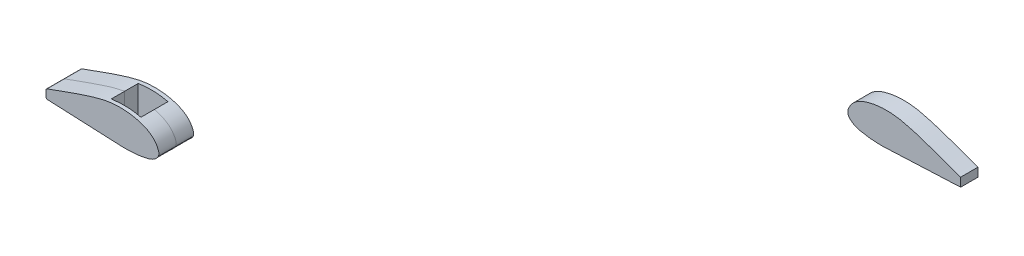
SolidWorks part; units mm, degrees
ref_plane "Front Plane" through (0, 0, 0) normal (0, 0, 1) x (1, 0, 0)
ref_plane "Top Plane" through (0, 0, 0) normal (0, 1, 0) x (1, 0, 0)
ref_plane "Right Plane" through (0, 0, 0) normal (1, 0, 0) x (0, 0, -1)
sketch "Sketch1" plane through (0, 0, 0) normal (0, 0, 1) x (1, 0, 0)
  line L0 (21.0546, 22.9864) -> (188.6881, 22.9864) construction
  line L1 (-41.685, 65.0353) -> (-41.685, -25.9647) construction
  line L3 (-116.1, 51.5887) -> (-116.1, -29.4113) construction
  line L4 (188.6881, 22.9864) -> (188.6881, 7.9864)
  spline S0 degree 3 poles (-151.9731, 22.9864) (-143.9092, 38.1196) (-120.835, 55.7856) (-80.169, 65.1927) (-35.3454, 65.9476) (18.9904, 59.1194) (95.9861, 45.5554) (152.0416, 30.4393) (188.6881, 22.9864) knots 0 0 0 0 0.141691 0.229555 0.346093 0.514874 0.687107 1 1 1 1
  spline S1 degree 3 poles (-151.9731, 22.9864) (-158.0316, 8.8512) (-149.1797, -22.7957) (-113.0152, -30.9858) (-83.4053, -30.4269) (17.4041, -20.5137) (107.6783, -0.9352) (188.6881, 7.9864) knots 0.008053 0.008053 0.008053 0.008053 0.128593 0.21014 0.276739 0.362962 1 1 1 1
  dimension "D1" = 81
  dimension "D2" = 91
  dimension "D3" = 15
  dimension "D4" = 343
sketch "Sketch2" plane through (0, 0, 0) normal (0, 0, 1) x (1, 0, 0)
  line L0 (582.2004, -1942.846) -> (4390.2004, -1942.846) construction
  line L1 (-5.98, 34.7326) -> (-5.98, -144.9211) construction
  line L2 (-106.6757, 91) -> (-106.6757, 0) construction
  line L3 (-106.6757, -0.5563) -> (-331.2996, 9.6091) construction
  line L6 (-332.8547, 9.4922) -> (-333.7996, 9.4922)
  line L7 (-331.2996, 9.6091) -> (-331.2996, 30.9254) construction
  line L8 (-106.7228, -3.0567) -> (-333.7996, 7.2197)
  line L9 (-333.7996, 7.2197) -> (-333.7996, 32.7336)
  spline S0 degree 3 poles (-331.2996, 30.9254) (-297.8418, 41.9545) (-253.3184, 59.9912) (-192.0547, 79.1992) (-150.6233, 90.2689) (-105.419, 92.3488) (-66.9278, 86.5323) (-36.0326, 74.7384) (-17.6589, 59.785) (-9.3021, 45.7524) (-5.5377, 35.7501) (-6.0018, 28.3147) (-10.6346, 20.776) (-24.032, 9.0194) (-45.4687, 4.5344) (-65.0902, 1.3964) (-83.8001, -0.2358) (-97.0071, -0.4829) (-106.6757, -0.5563) knots 0 0 0 0 0.223979 0.304379 0.408089 0.495215 0.589887 0.653497 0.703277 0.736722 0.756369 0.77031 0.782152 0.8116 0.880896 0.916077 0.938587 1 1 1 1 construction
  spline S1 degree 1 poles (-333.7996, 32.7336) (-106.7228, -3.0567) knots 0 0 1 1 construction
  spline S2 degree 3 poles (-333.7996, 32.7336) (-329.1237, 34.275) (-319.7928, 37.4124) (-301.2125, 43.9934) (-278.0532, 52.5474) (-250.2121, 62.8152) (-222.1096, 72.4601) (-193.7214, 81.1587) (-169.6947, 87.6921) (-150.0856, 91.4139) (-135.1756, 93.1815) (-120.1695, 93.9012) (-105.1423, 93.5955) (-90.1647, 92.2678) (-75.3139, 89.8335) (-60.6934, 86.2283) (-46.3415, 81.3284) (-34.9563, 75.6439) (-26.4496, 69.8498) (-20.5296, 64.8692) (-15.2153, 59.2269) (-10.6969, 52.9306) (-7.6128, 47.2762) (-5.4907, 42.5802) (-4.1355, 38.7998) (-3.3219, 34.7152) (-3.3391, 31.094) (-3.8981, 28.2134) (-4.898, 25.4017) (-6.7335, 22.3984) (-9.223, 19.2822) (-12.0263, 16.4329) (-15.0689, 13.8979) (-19.3823, 10.9122) (-25.1173, 7.9216) (-32.3596, 5.2763) (-39.8012, 3.3242) (-47.2993, 1.8347) (-54.6819, 0.548) (-62.0495, -0.6004) (-69.4829, -1.4996) (-79.4416, -2.3326) (-91.8643, -2.8893) (-101.7664, -3.0191) (-106.7228, -3.0567) knots -0.003832 -0.003832 -0.003832 -0.003832 0.027542 0.058916 0.121664 0.184413 0.247161 0.309909 0.372657 0.404031 0.435406 0.46678 0.498154 0.529528 0.560902 0.592276 0.62365 0.655024 0.670712 0.686399 0.702086 0.717773 0.73346 0.741303 0.749147 0.75699 0.764834 0.768756 0.772677 0.780521 0.788364 0.796208 0.804052 0.811895 0.827582 0.843269 0.858956 0.874643 0.89033 0.906017 0.921705 0.937392 0.968766 1.00014 1.00014 1.00014 1.00014
  dimension "D1" = 2.5
  dimension "D2" = 91
extrude "Boss-Extrude2" add sketch "Sketch2" along normal blind 50.8 separate body
fillet "Fillet2" radius 5 2 edges at (-333.7996, 7.2197, 25.4) (-333.7996, 32.7336, 25.4)
sketch "Sketch4" plane through (0, 0, 50.8) normal (0, 0, 1) x (1, 0, 0)
  line L0 (-67.2474, 87.7878) -> (-67.2474, -1.2122)
  line L1 (-154.2474, 90.5559) -> (-154.2474, -0.906)
  line L2 (-106.7228, -3.0567) -> (-329.0256, 7.0036) construction
  spline S0 degree 3 poles (-330.3793, 33.8668) (-326.848, 35.0427) (-318.6596, 37.8137) (-301.2125, 43.9934) (-278.0532, 52.5474) (-250.2121, 62.8152) (-222.1096, 72.4601) (-193.7214, 81.1587) (-169.6947, 87.6921) (-150.0856, 91.4139) (-135.1756, 93.1815) (-120.1695, 93.9012) (-105.1423, 93.5955) (-90.1647, 92.2678) (-75.3139, 89.8335) (-60.6934, 86.2283) (-46.3415, 81.3284) (-34.9563, 75.6439) (-26.4496, 69.8498) (-20.5296, 64.8692) (-15.2153, 59.2269) (-10.6969, 52.9306) (-7.6128, 47.2762) (-5.4907, 42.5802) (-4.1355, 38.7998) (-3.3219, 34.7152) (-3.3391, 31.094) (-3.8981, 28.2134) (-4.898, 25.4017) (-6.7335, 22.3984) (-9.223, 19.2822) (-12.0263, 16.4329) (-15.0689, 13.8979) (-19.3823, 10.9122) (-25.1173, 7.9216) (-32.3596, 5.2763) (-39.8012, 3.3242) (-47.2993, 1.8347) (-54.6819, 0.548) (-62.0495, -0.6004) (-69.4829, -1.4996) (-79.4416, -2.3326) (-91.8643, -2.8893) (-101.7664, -3.0191) (-106.7228, -3.0567) knots 0.003822 0.003822 0.003822 0.003822 0.027542 0.058916 0.121664 0.184413 0.247161 0.309909 0.372657 0.404031 0.435406 0.46678 0.498154 0.529528 0.560902 0.592276 0.62365 0.655024 0.670712 0.686399 0.702086 0.717773 0.73346 0.741303 0.749147 0.75699 0.764834 0.768756 0.772677 0.780521 0.788364 0.796208 0.804052 0.811895 0.827582 0.843269 0.858956 0.874643 0.89033 0.906017 0.921705 0.937392 0.968766 1.00014 1.00014 1.00014 1.00014 construction
  dimension "D1" = 87
  dimension "D2" = 89
sketch "Sketch5" plane through (0, 0, 0) normal (0, 1, 0) x (1, 0, 0)
  line L0 (-154.2474, -50.8) -> (-154.2474, -11.3)
  line L1 (-106.7228, -50.8) -> (-329.0256, -50.8) construction
  line L2 (-154.2474, -11.3) -> (-67.2474, -11.3)
  line L3 (-67.2474, -11.3) -> (-67.2474, -50.8)
  line L4 (-330.3793, -50.8) -> (-3.3709, -50.8) construction
  line L5 (-3.3709, 0) -> (-330.3793, 0) construction
  line L6 (-154.2474, -50.8) -> (-67.2474, -50.8)
  point P6 (-67.2474, -50.8)
  dimension "D1" = 87
  dimension "D2" = 11.3
extrude "Cut-Extrude1" cut sketch "Sketch5" against normal through all both and the other way through all
sketch "Sketch7" plane through (0, 0, 11.3) normal (0, 0, 1) x (1, 0, 0)
  line L0 (-154.2474, -0.906) -> (-106.7228, -3.0567) construction
  line L1 (-154.2474, -0.906) -> (-106.7228, -3.0567)
  line L2 (-154.2474, -0.906) -> (-154.2474, 4.7878)
  line L3 (-154.2474, 90.5559) -> (-154.2474, -0.906) construction
  line L4 (-154.2474, 4.7878) -> (-67.2474, 4.7878)
  line L5 (-67.2474, 87.7878) -> (-67.2474, -1.2122) construction
  line L6 (-67.2474, 4.7878) -> (-67.2474, -1.2122)
  spline S0 degree 3 poles (-2112.4086, -4538.979) (-528.9752, 150.7515) (-315.4023, -12.9058) (-79.4416, -2.3326) (172.6666, 18.7546) (361.4737, 490.2368) (-4320.865, -2623.6355) knots -0.494407 -0.494407 -0.494407 -0.494407 0.948356 0.97973 0.995417 2.536856 2.536856 2.536856 2.536856 only from (-106.7228, -3.0567) to (-67.2474, -1.2122) construction
  spline S1 degree 3 poles (-106.7228, -3.0567) (-101.7664, -3.0191) (-91.8643, -2.8893) (-79.4416, -2.3326) (-71.2231, -1.6452) (-67.9939, -1.2968) (-67.2474, -1.2122) knots 0.916982 0.916982 0.916982 0.916982 0.948356 0.97973 0.995417 1.00014 1.00014 1.00014 1.00014
  dimension "D1" = 6
extrude "Boss-Extrude4" add sketch "Sketch7" along normal up to surface (39.5 mm away) separate body up to face at (-287.5554, 23.8153, 50.8)
mirror "Mirror1" about plane through (0, 0, 50.8) normal (0, 0, 1) of bodies 112 115
sketch "Sketch6" plane through (0, 0, 0) normal (0, 0, -1) x (-1, 0, 0)
  line L0 (-1325.5933, -930.3083) -> (2482.4067, -930.3083) construction
  line L1 (-1913.7737, 1047.2703) -> (-1913.7737, 867.6166) construction
  line L2 (-2014.4694, 1103.5378) -> (-2014.4694, 1012.5378) construction
  line L3 (-2014.4694, 1011.9814) -> (-2239.0933, 1022.1468) construction
  line L6 (-2240.6484, 1022.03) -> (-2241.5933, 1022.03)
  line L7 (-2239.0933, 1022.1468) -> (-2239.0933, 1043.4632) construction
  line L8 (-2014.5165, 1009.481) -> (-2241.5933, 1019.7574)
  line L9 (-2241.5933, 1019.7574) -> (-2241.5933, 1045.2714)
  spline S0 degree 3 poles (-2239.0933, 1043.4632) (-2205.6355, 1054.4923) (-2161.1121, 1072.5289) (-2099.8485, 1091.7369) (-2058.417, 1102.8066) (-2013.2127, 1104.8866) (-1974.7215, 1099.07) (-1943.8264, 1087.2762) (-1925.4526, 1072.3228) (-1917.0958, 1058.2902) (-1913.3314, 1048.2878) (-1913.7955, 1040.8525) (-1918.4283, 1033.3137) (-1931.8257, 1021.5571) (-1953.2624, 1017.0722) (-1972.8839, 1013.9342) (-1991.5938, 1012.302) (-2004.8009, 1012.0549) (-2014.4694, 1011.9814) knots 0 0 0 0 0.223979 0.304379 0.408089 0.495215 0.589887 0.653497 0.703277 0.736722 0.756369 0.77031 0.782152 0.8116 0.880896 0.916077 0.938587 1 1 1 1 construction
  spline S1 degree 1 poles (-2241.5933, 1045.2714) (-2014.5165, 1009.481) knots 0 0 1 1 construction
  spline S2 degree 3 poles (-2241.5933, 1045.2714) (-2236.9174, 1046.8127) (-2227.5865, 1049.9501) (-2209.0062, 1056.5311) (-2185.8469, 1065.0851) (-2158.0058, 1075.3529) (-2129.9033, 1084.9979) (-2101.5151, 1093.6964) (-2077.4884, 1100.2299) (-2057.8794, 1103.9516) (-2042.9693, 1105.7192) (-2027.9632, 1106.4389) (-2012.9361, 1106.1333) (-1997.9584, 1104.8056) (-1983.1076, 1102.3713) (-1968.4872, 1098.766) (-1954.1352, 1093.8661) (-1942.7501, 1088.1817) (-1934.2433, 1082.3875) (-1928.3233, 1077.4069) (-1923.0091, 1071.7646) (-1918.4907, 1065.4683) (-1915.4065, 1059.8139) (-1913.2844, 1055.118) (-1911.9292, 1051.3376) (-1911.1156, 1047.253) (-1911.1328, 1043.6318) (-1911.6918, 1040.7512) (-1912.6917, 1037.9394) (-1914.5272, 1034.9361) (-1917.0167, 1031.82) (-1919.82, 1028.9707) (-1922.8627, 1026.4357) (-1927.176, 1023.45) (-1932.911, 1020.4594) (-1940.1533, 1017.814) (-1947.5949, 1015.862) (-1955.093, 1014.3724) (-1962.4756, 1013.0857) (-1969.8432, 1011.9374) (-1977.2767, 1011.0381) (-1987.2353, 1010.2051) (-1999.658, 1009.6485) (-2009.5601, 1009.5186) (-2014.5165, 1009.481) knots -0.003832 -0.003832 -0.003832 -0.003832 0.027542 0.058916 0.121664 0.184413 0.247161 0.309909 0.372657 0.404031 0.435406 0.46678 0.498154 0.529528 0.560902 0.592276 0.62365 0.655024 0.670712 0.686399 0.702086 0.717773 0.73346 0.741303 0.749147 0.75699 0.764834 0.768756 0.772677 0.780521 0.788364 0.796208 0.804052 0.811895 0.827582 0.843269 0.858956 0.874643 0.89033 0.906017 0.921705 0.937392 0.968766 1.00014 1.00014 1.00014 1.00014
  dimension "D1" = 2.5
  dimension "D2" = 91
extrude "Boss-Extrude3" add sketch "Sketch6" along normal blind 50.8 separate body
sketch "Sketch8" plane through (0, 0, 101.6) normal (0, 0, 1) x (1, 0, 0)
  line L2 (-329.0256, 7.0036) -> (-106.7228, -3.0567)
  line L3 (-333.7996, 29.1229) -> (-333.7996, 11.9985)
  line L4 (-329.0256, 7.0036) -> (-106.7228, -3.0567)
  line L5 (-333.7996, 29.1229) -> (-333.7996, 11.9985)
  arc A2 (-330.3793, 33.8668) -> (-333.7996, 29.1229) centre (-328.7996, 29.1229) ccw
  arc A3 (-333.7996, 11.9985) -> (-329.0256, 7.0036) centre (-328.7996, 11.9985) ccw
  arc A4 (-330.3793, 33.8668) -> (-333.7996, 29.1229) centre (-328.7996, 29.1229) ccw
  arc A5 (-333.7996, 11.9985) -> (-329.0256, 7.0036) centre (-328.7996, 11.9985) ccw
  spline S1 degree 3 poles (-1455.9216, -2650.1227) (-462.0432, 104.0457) (-279.0809, -11.2783) (-79.4416, -2.3326) (-69.4829, -1.4996) (-62.0495, -0.6004) (-54.6819, 0.548) (-47.2993, 1.8347) (-39.8012, 3.3242) (-32.3596, 5.2763) (-25.1173, 7.9216) (-19.3823, 10.9122) (-15.0689, 13.8979) (-12.0263, 16.4329) (-9.223, 19.2822) (-6.7335, 22.3984) (-4.898, 25.4017) (-3.8981, 28.2134) (-3.3391, 31.094) (-3.3219, 34.7152) (-4.1355, 38.7998) (-5.4907, 42.5802) (-7.6128, 47.2762) (-10.6969, 52.9306) (-15.2153, 59.2269) (-20.5296, 64.8692) (-26.4496, 69.8498) (-34.9563, 75.6439) (-46.3415, 81.3284) (-60.6934, 86.2283) (-75.3139, 89.8335) (-90.1647, 92.2678) (-105.1423, 93.5955) (-120.1695, 93.9012) (-135.1756, 93.1815) (-150.0856, 91.4139) (-169.6947, 87.6921) (-193.7214, 81.1587) (-222.1096, 72.4601) (-250.2121, 62.8152) (-278.0532, 52.5474) (-301.2125, 43.9934) (-613.19, -66.5065) (-959.1387, -11.1755) (-1396.5791, -2690.767) knots -1.178239 -1.178239 -1.178239 -1.178239 0.035196 0.06657 0.082257 0.097944 0.113631 0.129318 0.145005 0.160693 0.17638 0.192067 0.19991 0.207754 0.215597 0.223441 0.231284 0.235206 0.239128 0.246971 0.254815 0.262658 0.270502 0.286189 0.301876 0.317563 0.33325 0.348937 0.380311 0.411686 0.44306 0.474434 0.505808 0.537182 0.568556 0.59993 0.631304 0.694053 0.756801 0.819549 0.882297 0.945046 0.97642 2.989478 2.989478 2.989478 2.989478 only from (-106.7228, -3.0567) to (-330.3793, 33.8668)
  spline S2 degree 3 poles (-106.7228, -3.0567) (-101.7664, -3.0191) (-91.8643, -2.8893) (-79.4416, -2.3326) (-69.4829, -1.4996) (-62.0495, -0.6004) (-54.6819, 0.548) (-47.2993, 1.8347) (-39.8012, 3.3242) (-32.3596, 5.2763) (-25.1173, 7.9216) (-19.3823, 10.9122) (-15.0689, 13.8979) (-12.0263, 16.4329) (-9.223, 19.2822) (-6.7335, 22.3984) (-4.898, 25.4017) (-3.8981, 28.2134) (-3.3391, 31.094) (-3.3219, 34.7152) (-4.1355, 38.7998) (-5.4907, 42.5802) (-7.6128, 47.2762) (-10.6969, 52.9306) (-15.2153, 59.2269) (-20.5296, 64.8692) (-26.4496, 69.8498) (-34.9563, 75.6439) (-46.3415, 81.3284) (-60.6934, 86.2283) (-75.3139, 89.8335) (-90.1647, 92.2678) (-105.1423, 93.5955) (-120.1695, 93.9012) (-135.1756, 93.1815) (-150.0856, 91.4139) (-169.6947, 87.6921) (-193.7214, 81.1587) (-222.1096, 72.4601) (-250.2121, 62.8152) (-278.0532, 52.5474) (-301.2125, 43.9934) (-318.6596, 37.8137) (-326.848, 35.0427) (-330.3793, 33.8668) knots 0.003822 0.003822 0.003822 0.003822 0.035196 0.06657 0.082257 0.097944 0.113631 0.129318 0.145005 0.160693 0.17638 0.192067 0.19991 0.207754 0.215597 0.223441 0.231284 0.235206 0.239128 0.246971 0.254815 0.262658 0.270502 0.286189 0.301876 0.317563 0.33325 0.348937 0.380311 0.411686 0.44306 0.474434 0.505808 0.537182 0.568556 0.59993 0.631304 0.694053 0.756801 0.819549 0.882297 0.945046 0.97642 1.00014 1.00014 1.00014 1.00014
  dimension "D1" = 0
